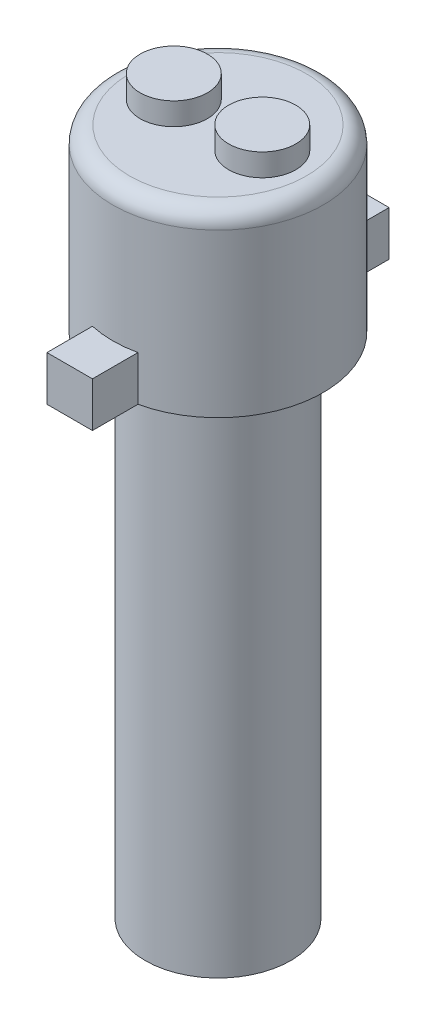
SolidWorks part; units mm, degrees
ref_plane "Front Plane" through (0, 0, 0) normal (0, 0, 1) x (1, 0, 0)
ref_plane "Top Plane" through (0, 0, 0) normal (0, 1, 0) x (1, 0, 0)
ref_plane "Right Plane" through (0, 0, 0) normal (1, 0, 0) x (0, 0, -1)
sketch "Sketch1" plane through (0, 0, 0) normal (0, 1, 0) x (1, 0, 0)
  circle A0 centre (0, 0) radius 3.25
  dimension "D1" = 6.5
extrude "Boss-Extrude1" add sketch "Sketch1" along normal blind 22.686 contours A0
sketch "Sketch2" plane through (0, 0, 0) normal (0, -1, 0) x (1, 0, 0)
  circle A1 centre (0, 0) radius 1.75
  dimension "D1" = 3.5
extrude "Cut-Extrude1" [suppressed] cut sketch "Sketch2" against normal blind 2.5
sketch "Sketch6" plane through (0, 22.686, 0) normal (0, 1, 0) x (1, 0, 0)
  circle A0 centre (0, 0) radius 4.7
  dimension "D1" = 9.4
extrude "Boss-Extrude2" add sketch "Sketch6" along normal blind 8 contours A0
fillet "Fillet2" radius 0.75 1 edges at (0, 30.686, 4.7)
sketch "Sketch7" plane through (0, 30.686, 0) normal (0, 1, 0) x (1, 0, 0)
  line L0 (3.95, 0) -> (0, 0) construction
  line L1 (0, 0) -> (-3.95, 0) construction
  line L2 (0, 0) -> (1.975, 0) construction
  line L3 (0, 0) -> (-1.975, 0) construction
  circle A0 centre (0, 0) radius 3.95 construction
  circle A1 centre (-1.975, 0) radius 1.5
  circle A2 centre (1.975, 0) radius 1.5
  dimension "D1" = 3
  dimension "D2" = 3
extrude "Boss-Extrude3" add sketch "Sketch7" along normal blind 1
sketch "Sketch8" plane through (0, 22.686, 0) normal (0, -1, 0) x (1, 0, 0)
  line L0 (0, 4.7) -> (0, -4.7) construction
  line L1 (-1.016, 4.5889) -> (-1.016, 6.6209)
  line L2 (-1.016, 6.6209) -> (1.016, 6.6209)
  line L3 (1.016, 6.6209) -> (1.016, 4.5889)
  line L4 (-4.7, 0) -> (4.7, 0) construction
  line L5 (1.016, -6.6209) -> (1.016, -4.5889)
  line L6 (-1.016, -6.6209) -> (1.016, -6.6209)
  line L7 (-1.016, -4.5889) -> (-1.016, -6.6209)
  circle A0 centre (0, 0) radius 4.7 construction
  arc A1 (1.016, 4.5889) -> (-1.016, 4.5889) centre (0, 0) ccw
  arc A2 (1.016, -4.5889) -> (-1.016, -4.5889) centre (0, 0) cw
  dimension "D1" = 2.032
  dimension "D2" = 2.032
extrude "Boss-Extrude4" add sketch "Sketch8" against normal blind 2
